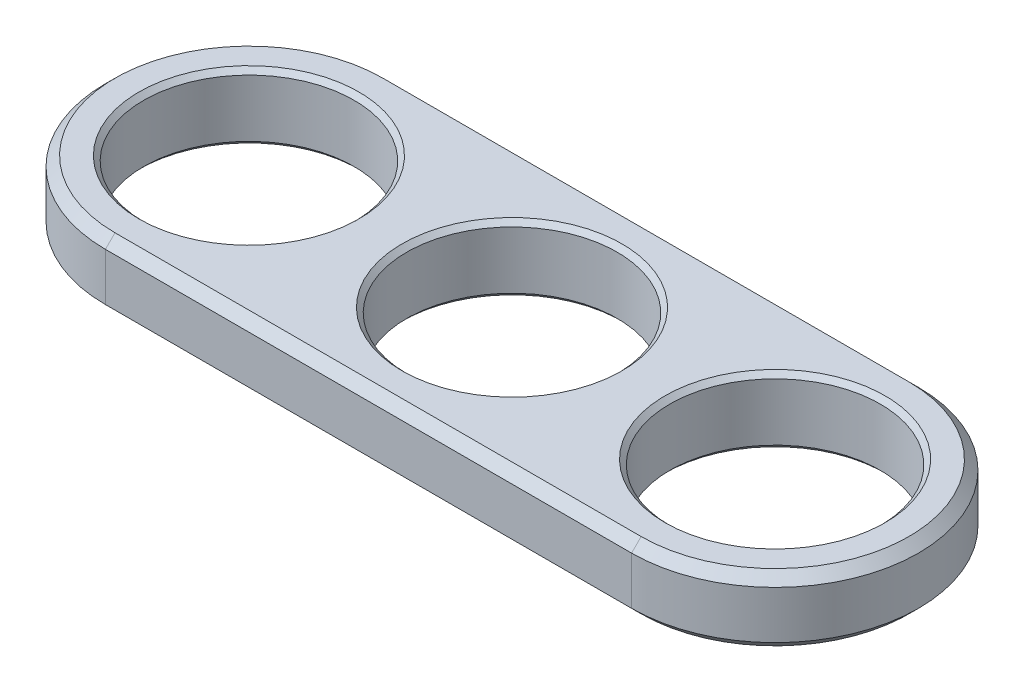
SolidWorks part; units mm, degrees
ref_plane "Plan de face" through (0, 0, 0) normal (0, 0, 1) x (1, 0, 0)
ref_plane "Plan de dessus" through (0, 0, 0) normal (0, 1, 0) x (1, 0, 0)
ref_plane "Plan de droite" through (0, 0, 0) normal (1, 0, 0) x (0, 0, -1)
sketch "Esquisse1" plane through (0, 0, 0) normal (0, 1, 0) x (1, 0, 0)
  line L0 (0, 0) -> (55, 0) construction
  line L1 (0, 15) -> (55, 15)
  line L2 (0, -15) -> (55, -15)
  arc A0 (0, 15) -> (0, -15) centre (0, 0) ccw
  arc A1 (55, -15) -> (55, 15) centre (55, 0) ccw
  circle A2 centre (27.5, 0) radius 11
  circle A3 centre (0, 0) radius 11
  circle A4 centre (55, 0) radius 11
  point P3 (27.5, 0)
  dimension "D1" = 22
  dimension "D2" = 22
  dimension "D3" = 22
extrude "Boss.-Extru.1" add sketch "Esquisse1" along normal blind 7
chamfer "Chanfrein1" distance 0.5 angle 45 6 edges at (55, 0, 11) (55, 7, 11) (27.5, 0, 11) (27.5, 7, 11) (0, 0, 11) (0, 7, 11)
chamfer "Chanfrein2" distance 1 angle 45 8 edges at (27.5, 0, -15) (-15, 0, 0) (70, 0, 0) (27.5, 0, 15) (27.5, 7, -15) (-15, 7, 0) (70, 7, 0) (27.5, 7, 15)
